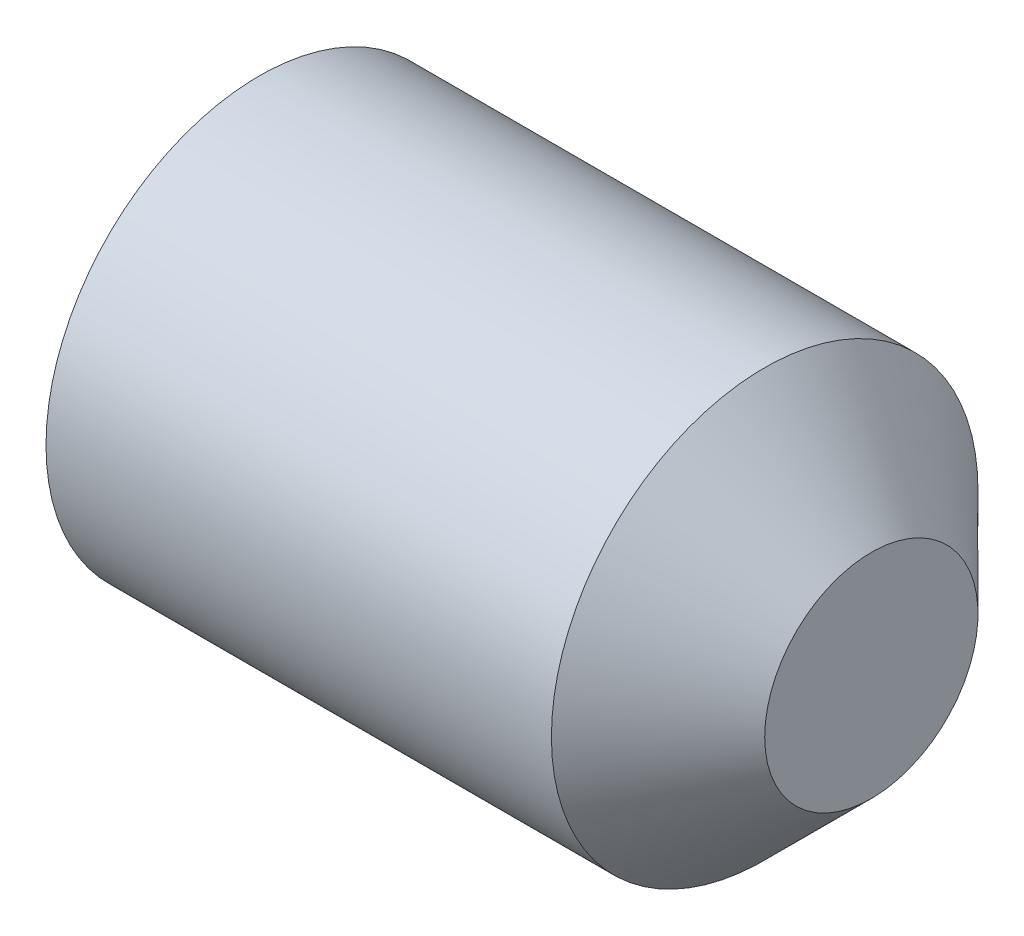
SolidWorks part; units mm, degrees
ref_plane "Plane1" through (0, 0, 0) normal (0, 0, 1) x (1, 0, 0)
ref_plane "Plane2" through (0, 0, 0) normal (0, 1, 0) x (1, 0, 0)
ref_plane "Plane3" through (0, 0, 0) normal (1, 0, 0) x (0, 0, -1)
sketch "BodySke" plane through (0, 0, 0) normal (0, 0, 1) x (1, 0, 0)
  line L0 (0, 0) -> (0, 0.774)
  line L1 (0, 0.774) -> (0.1305, 1)
  line L2 (0.1305, 1) -> (2.5, 1)
  line L3 (2.5, 1) -> (3, 0.5)
  line L4 (3, 0) -> (0, 0)
  line L5 (-12.7, 0) -> (88.9, 0) construction
  line L6 (3, 0.5) -> (3, 0)
  line L7 (3, 0.5) -> (3, 10.025) construction
  line L8 (0, -0.774) -> (0.1305, -1) construction
  line L9 (0.4, 15.875) -> (0.4, -3.175) construction
  line L10 (2.5, -1) -> (3, -0.5) construction
  dimension "Length" = 3
  dimension "Diameter" = 2
  dimension "Drive_ch_ang" = 60
  dimension "Minor_dia" = 1.548
  dimension "Cup_nose_ang" = 45
  dimension "Cup_dia" = 1
  dimension "Advance" = 0.4
revolve "BaseBody" add sketch "BodySke" angle 360 about L5
cosmetic thread "ThreadCosmetic" parameters "Thread_minor"=1.548
sketch "Sketch2" plane through (0, 0, 0) normal (-1, 0, 0) x (0, 0, 1)
  line L0 (0.2598, 0.45) -> (-0.2598, 0.45)
  line L1 (-0.2598, 0.45) -> (-0.5196, 0)
  line L2 (0.2598, 0.45) -> (0.5196, 0)
  line L3 (0.2598, -0.45) -> (0.5196, 0)
  line L4 (0.2598, -0.45) -> (-0.2598, -0.45)
  line L5 (-0.2598, -0.45) -> (-0.5196, 0)
  dimension "Hex_size" = 0.9
  dimension "D2" = 0.45
  dimension "D3" = 0.45
extrude "Hex" cut sketch "Sketch2" against normal blind 0.8
sketch "ThdSchSke" plane through (0, 0, 0) normal (0, 0, 1) x (1, 0, 0)
  line L0 (0.1305, -0.774) -> (-0.0278, -1)
  line L1 (0.1305, -0.774) -> (0.2887, -1)
  line L2 (0.2887, -1) -> (0.2887, -1.25)
  line L3 (-3.175, 0) -> (5.1513, 0) construction
  line L5 (0.2887, -1.25) -> (-0.0278, -1.25)
  line L6 (-0.0278, -1.25) -> (-0.0278, -1)
  line L8 (0.1305, 1) -> (0.1305, -1) construction
  dimension "Thread_minor" = 1.548
  dimension "Diameter" = 2
  dimension "SideAngle" = 55
  dimension "VeeAngle" = 70
  dimension "Overcut" = 2.5
revolve "ThreadSchematic" [suppressed] cut sketch "ThdSchSke" angle 360 about L3
pattern_linear "ThdSchPat" [suppressed]
equation "\"D2@Sketch2\" = \"Hex_size@Sketch2\" / 2"
equation "\"D3@Sketch2\" = \"Hex_size@Sketch2\" / 2"
equation "\"Thread_minor@ThreadCosmetic\" = \"Minor_dia@BodySke\""
equation "\"Thread_minor@ThdSchSke\" = \"Thread_minor@ThreadCosmetic\""
equation "\"Diameter@ThdSchSke\" = \"Diameter@BodySke\""
equation "\"Overcut@ThdSchSke\" = \"Diameter@BodySke\" * 1.25"
equation "\"Num_threads@ThdSchPat\" = int( (\"Length@BodySke\" - ( ( ( \"Diameter@BodySke\" - \"Minor_dia@BodySke\" ) * 0.5 ) / tan( \"Drive_ch_ang@BodySke\" * 0.017453292 ) ) - ( ( ( \"Diameter@BodySke\" - \"Cup_dia@BodySke\" ) * 0.5 ) * tan( \"Cup_nose_ang@BodySke\" * 0.017453292 ) ) ) / \"Advance@BodySke\" + 0.999 )  + 1"
equation "\"Advance@ThdSchPat\" = (\"Length@BodySke\" - ( ( ( \"Diameter@BodySke\" - \"Minor_dia@BodySke\" ) * 0.5 ) / tan( \"Drive_ch_ang@BodySke\" * 0.017453292 ) ) - ( ( ( \"Diameter@BodySke\" - \"Cup_dia@BodySke\" ) * 0.5 ) * tan( \"Cup_nose_ang@BodySke\" * 0.017453292 ) ) ) /  (\"Num_threads@ThdSchPat\" - 1) 'relax it"
equation "' \"Num_threads@ThdSchPat\" = \"Num_threads@ThdSchPat\" - sgn( \"Num_threads@ThdSchPat\" - 1) '---chamfered tips only---"
